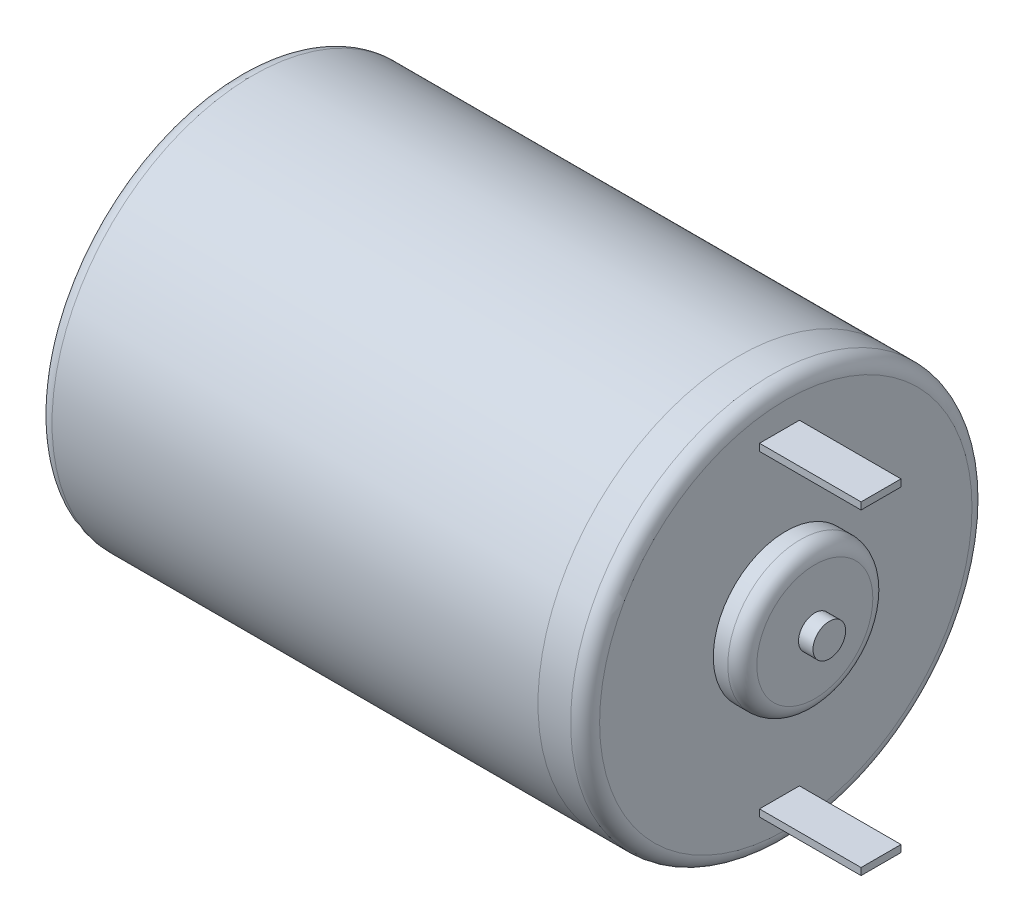
SolidWorks part; units mm, degrees
ref_plane "Front Plane" through (0, 0, 0) normal (0, 0, 1) x (1, 0, 0)
ref_plane "Top Plane" through (0, 0, 0) normal (0, 1, 0) x (1, 0, 0)
ref_plane "Right Plane" through (0, 0, 0) normal (1, 0, 0) x (0, 0, -1)
sketch "Sketch1" plane through (0, 0, 0) normal (1, 0, 0) x (0, 0, -1)
  circle A0 centre (0, 0) radius 13.835
  dimension "D1" = 27.67
extrude "Boss-Extrude1" add sketch "Sketch1" along normal blind 34.5
sketch "Sketch2" plane through (34.5, 0, 0) normal (1, 0, 0) x (0, 0, -1)
  circle A0 centre (0, 0) radius 13.835
extrude "Boss-Extrude2" add sketch "Sketch2" along normal blind 3.25 separate body
sketch "Sketch3" plane through (37.75, 0, 0) normal (1, 0, 0) x (0, 0, -1)
  circle A0 centre (0, 0) radius 5
extrude "Boss-Extrude3" add sketch "Sketch3" along normal blind 2
fillet "Fillet1" radius 1 1 edges at (0, 0, -13.835)
sketch "Sketch4" plane through (39.75, 0, 0) normal (1, 0, 0) x (0, 0, -1)
  circle A0 centre (0, 0) radius 1.125
extrude "Boss-Extrude4" add sketch "Sketch4" along normal blind 1
fillet "Fillet2" radius 1 2 edges at (39.75, 0, -5) (37.75, 0, -13.835)
sketch "Sketch5" plane through (37.75, 0, 0) normal (1, 0, 0) x (0, 0, -1)
  line L1 (0.9384, -11.1569) -> (-1.8116, -11.1569)
  line L2 (0.9384, -11.1569) -> (0.9384, -10.6714)
  line L3 (0.9384, -10.6714) -> (-1.8116, -10.6714)
  line L4 (-1.8116, -11.1569) -> (-1.8116, -10.6714)
  dimension "D1" = 2.75
extrude "Boss-Extrude5" add sketch "Sketch5" along normal blind 7
mirror "Mirror1" about plane through (0, 0, 0) normal (0, 1, 0) of "Boss-Extrude5"
